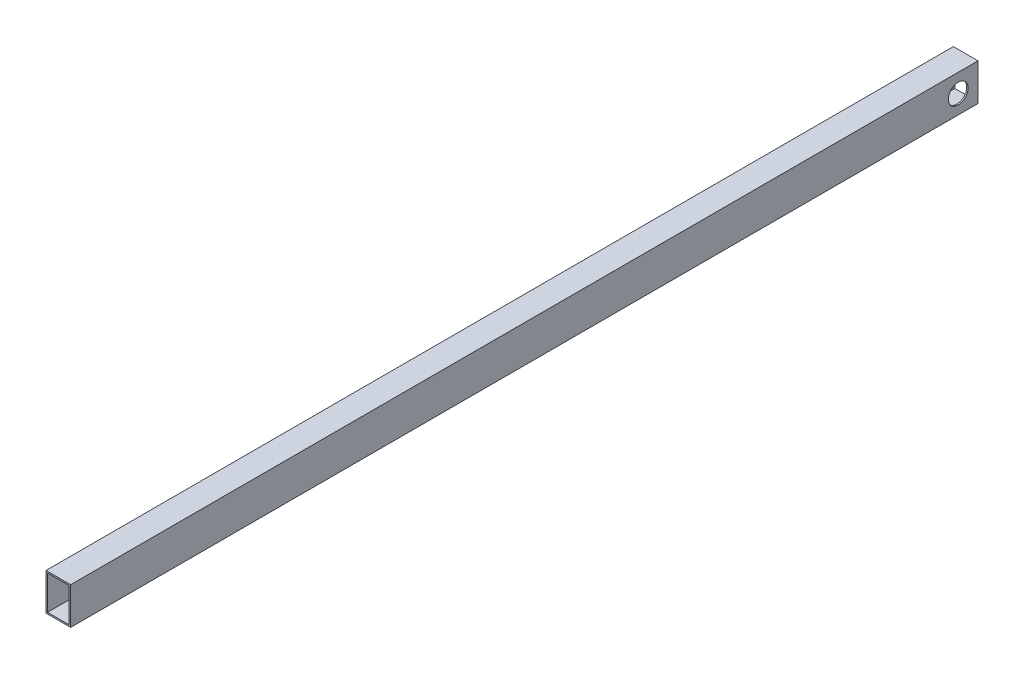
SolidWorks part; units mm, degrees
material "Plain Carbon Steel"
ref_plane "Front Plane" through (0, 0, 0) normal (0, 0, 1) x (1, 0, 0)
ref_plane "Top Plane" through (0, 0, 0) normal (0, 1, 0) x (1, 0, 0)
ref_plane "Right Plane" through (0, 0, 0) normal (1, 0, 0) x (0, 0, -1)
sketch "Sketch1" plane through (0, 0, 0) normal (0, 0, 1) x (1, 0, 0)
  line B0 (-50, -75) -> (50, -75)
  line B1 (-50, -75) -> (-50, 75)
  line B2 (50, -75) -> (50, 75)
  line B3 (-50, 75) -> (50, 75)
  line B4 (-44, -69) -> (44, -69)
  line B5 (-44, -69) -> (-44, 69)
  line B6 (44, -69) -> (44, 69)
  line B7 (-44, 69) -> (44, 69)
sketch_block_instance "15x10x6_profil-1"
sketch_block "15x10x6_profil" parameters "D1"=100, "D2"=150, "D3"=6, "D4"=6
extrude "Boss-Extrude1" add sketch "Sketch1" along normal blind 3600 and the other way blind 80
sketch "Sketch2" plane through (0, 0, 0) normal (1, 0, 0) x (0, 0, -1)
  circle A0 centre (0, 0) radius 40
  dimension "D1" = 80
extrude "Cut-Extrude1" cut sketch "Sketch2" against normal through all and the other way through all
